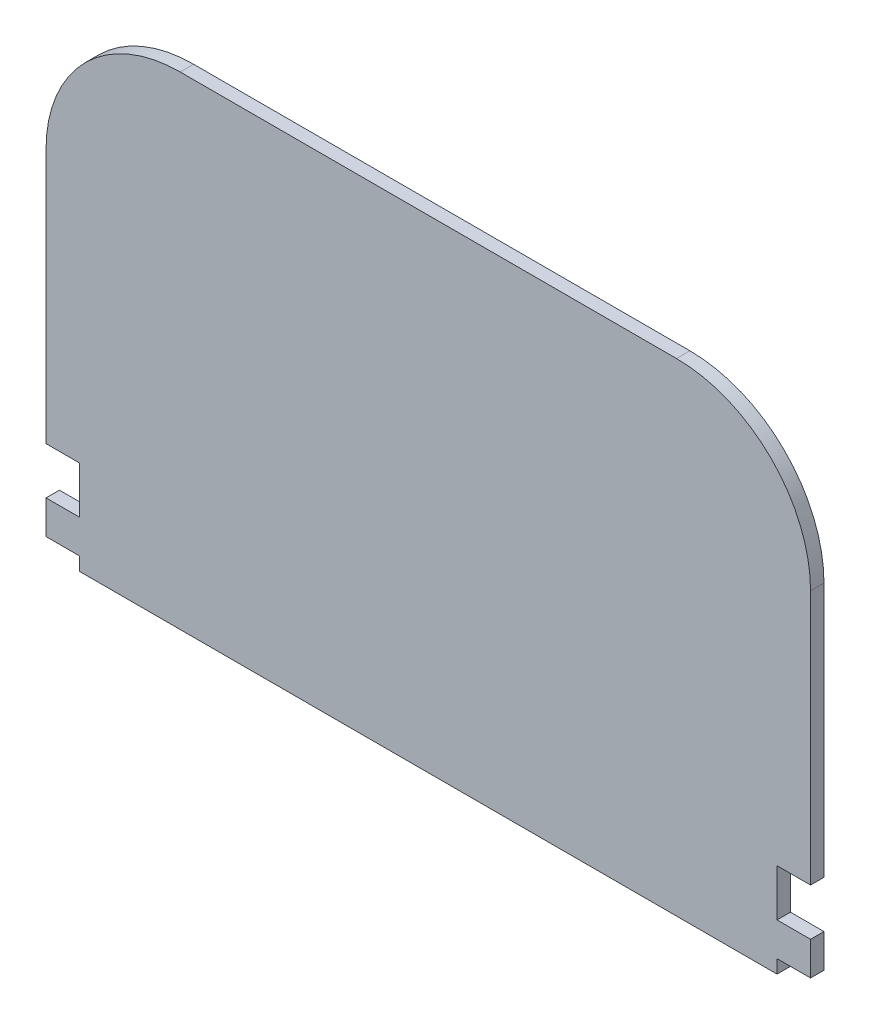
SolidWorks part; units mm, degrees
ref_plane "Front Plane" through (0, 0, 0) normal (0, 0, 1) x (1, 0, 0)
ref_plane "Top Plane" through (0, 0, 0) normal (0, 1, 0) x (1, 0, 0)
ref_plane "Right Plane" through (0, 0, 0) normal (1, 0, 0) x (0, 0, -1)
sketch "Sketch1" plane through (0, 0, 0) normal (0, 0, 1) x (1, 0, 0)
  line L0 (0, 1) -> (2.5, 1)
  line L1 (2.5, 0) -> (54.5, 0)
  line L2 (0, 1) -> (0, 3.5)
  line L3 (10, 36) -> (47, 36)
  line L4 (57, 1) -> (57, 3.5)
  line L5 (54.5, 0) -> (54.5, 1)
  line L6 (2.5, 0) -> (2.5, 1)
  line L7 (54.5, 1) -> (57, 1)
  line L8 (0, 0) -> (57, 0) construction
  line L9 (57, 0) -> (57, 26) construction
  line L10 (0, 0) -> (0, 26) construction
  line L11 (0, 7) -> (0, 26)
  line L12 (0, 1) -> (57, 1) construction
  line L13 (54.5, 3.5) -> (57, 3.5)
  line L14 (54, 3.5) -> (57, 3.5) construction
  line L15 (0, 3.5) -> (2.5, 3.5)
  line L16 (0, 7) -> (2.5, 7)
  line L17 (54.5, 7) -> (57, 7)
  line L18 (54, 7) -> (57, 7) construction
  line L19 (0, 3.5) -> (3, 3.5) construction
  line L20 (57, 7) -> (57, 26)
  line L21 (0, 7) -> (3, 7) construction
  line L22 (54.5, 3.5) -> (54.5, 7)
  line L23 (54.5, 0) -> (54.5, 26) construction
  line L24 (2.5, 3.5) -> (2.5, 7)
  line L26 (2.5, 0) -> (2.5, 26) construction
  arc A0 (47, 36) -> (57, 26) centre (47, 26) cw
  arc A1 (10, 36) -> (0, 26) centre (10, 26) ccw
  point P0 (0, 0)
  point P3 (57, 0)
  point P11 (54, 0)
  point P12 (54, 26)
  point P13 (3, 0)
  point P14 (3, 26)
extrude "Boss-Extrude1" add sketch "Sketch1" along normal blind 1
